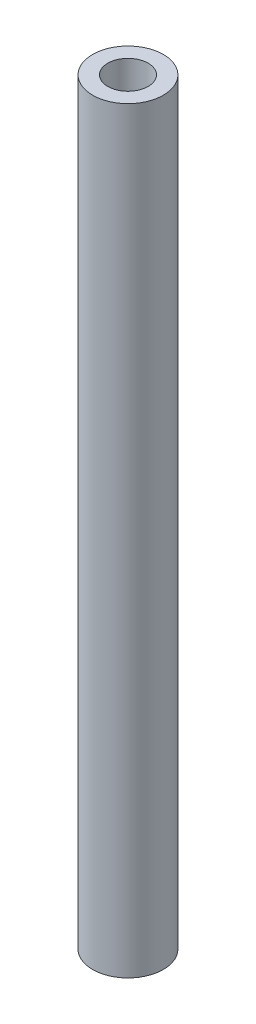
SolidWorks part; units mm, degrees
material "Gerais  - 6061-T6"
ref_plane "Plano frontal" through (0, 0, 0) normal (0, 0, 1) x (1, 0, 0)
ref_plane "Plano superior" through (0, 0, 0) normal (0, 1, 0) x (1, 0, 0)
ref_plane "Plano direito" through (0, 0, 0) normal (1, 0, 0) x (0, 0, -1)
ref_plane "Plano1" through (0, 0, 0) normal (0, 0, -1) x (-1, 0, 0)
sketch "Esboço1" plane through (0, 0, 0) normal (0, 0, -1) x (-1, 0, 0)
  line L0 (53.2146, -75) -> (54.7146, -75)
  line L1 (54.7146, -75) -> (54.7146, 0)
  line L2 (54.7146, 0) -> (53.2146, 0)
  line L3 (53.2146, 0) -> (53.2146, -75)
  line L4 (56.7146, -75) -> (56.7146, 0) construction
  dimension "D1" = 2
  dimension "D2" = 3.5
  dimension "D3" = 75
revolve "Revolução1" add sketch "Esboço1" angle 360 about L4
